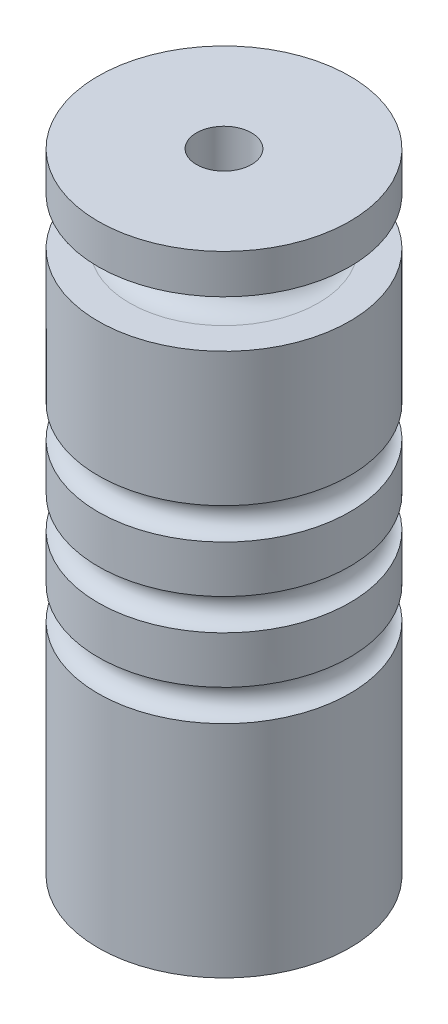
SolidWorks part; units mm, degrees
ref_plane "Front Plane" through (0, 0, 0) normal (0, 0, 1) x (1, 0, 0)
ref_plane "Top Plane" through (0, 0, 0) normal (0, 1, 0) x (1, 0, 0)
ref_plane "Right Plane" through (0, 0, 0) normal (1, 0, 0) x (0, 0, -1)
sketch "Sketch1" plane through (0, 0, 0) normal (0, 1, 0) x (1, 0, 0)
  circle A0 centre (0, 0) radius 8
extrude "Extrude1" add sketch "Sketch1" along normal blind 40
sketch "Sketch2" plane through (0, 40, 0) normal (0, 1, 0) x (-1, 0, 0)
  circle A0 centre (0, 0) radius 1.75
extrude "Extrude2" cut sketch "Sketch2" against normal blind 40
sketch "Sketch3" plane through (0, 0, 0) normal (0, -1, 0) x (1, 0, 0)
  circle A0 centre (0, 0) radius 4
extrude "Extrude3" cut sketch "Sketch3" against normal blind 6.35
sketch "Sketch4" plane through (0, 0, 0) normal (0, 0, 1) x (1, 0, 0)
  line L0 (8, 0) -> (8, 40) construction
  circle A0 centre (8, 20) radius 1
  circle A1 centre (8, 25) radius 1
  circle A2 centre (8, 15) radius 1
ref_plane "Plane1" through (0, 15, 0) normal (0, 1, 0) x (-1, 0, 0)
sketch "Sketch6" plane through (0, 15, 0) normal (0, 1, 0) x (-1, 0, 0)
  circle A0 centre (0, 0) radius 8
sweep "Cut-Sweep1" cut profiles "Sketch4" path "Sketch6"
ref_plane "Plane2" through (0, 36, 0) normal (0, 1, 0) x (-1, 0, 0)
sketch "Sketch8" plane through (0, 36, 0) normal (0, 1, 0) x (-1, 0, 0)
  circle A0 centre (0, 0) radius 6
sketch "Sketch9" plane through (0, 0, 0) normal (0, 0, 1) x (1, 0, 0)
  line L1 (8.5, 37.5) -> (6, 37.5)
  line L2 (8.5, 37.5) -> (8.5, 34.5)
  line L3 (8.5, 34.5) -> (6, 34.5)
  line L4 (6, 37.5) -> (6, 34.5)
sweep "Cut-Sweep3" cut profiles "Sketch9" path "Sketch8"
sketch "Sketch10" plane through (0, 0, 0) normal (0, 0, 1) x (1, 0, 0)
  circle A0 centre (6, 36) radius 1.5
sketch "Sketch11" plane through (0, 36, 0) normal (0, 1, 0) x (-1, 0, 0)
  circle A0 centre (0, 0) radius 6
sweep "Cut-Sweep4" cut profiles "Sketch10" path "Sketch11"
